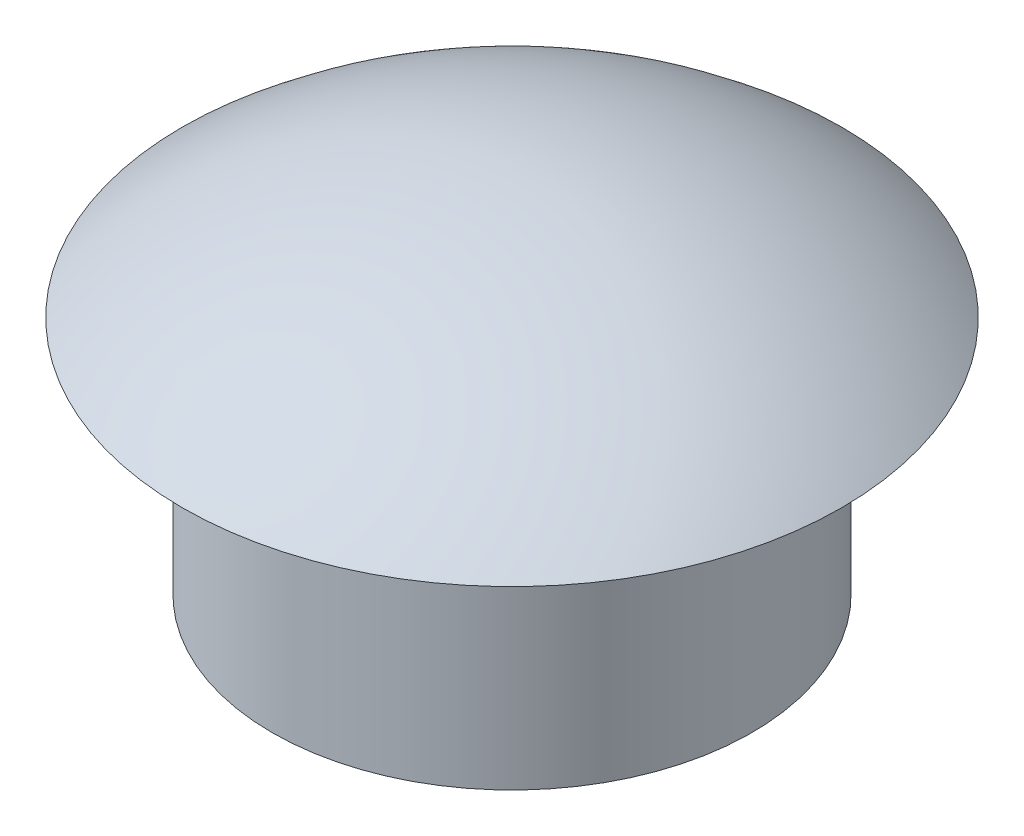
SolidWorks part; units mm, degrees
material "ABS PC"
ref_plane "Front Plane" through (0, 0, 0) normal (0, 0, 1) x (1, 0, 0)
ref_plane "Top Plane" through (0, 0, 0) normal (0, 1, 0) x (1, 0, 0)
ref_plane "Right Plane" through (0, 0, 0) normal (1, 0, 0) x (0, 0, -1)
sketch "Sketch1" plane through (0, 0, 0) normal (0, 1, 0) x (1, 0, 0)
  circle A0 centre (0, 0) radius 6.35
  circle A1 centre (0, 0) radius 4.7625
  dimension "D1" = 12.7
  dimension "D2" = 1.5875
extrude "Boss-Extrude1" add sketch "Sketch1" along normal blind 6.35
sketch "Sketch2" plane through (0, 0, 0) normal (0, 0, 1) x (1, 0, 0)
  line L0 (0, -55) -> (0, 55) construction
  line L1 (0, 9.525) -> (0, 6.35)
  line L2 (0, 6.35) -> (8.7312, 6.35)
  line L3 (6.35, 0) -> (6.35, 6.35) construction
  arc A0 (0, 9.525) -> (8.7312, 6.35) centre (0, -4.068) cw
  dimension "D1" = 3.175
  dimension "D2" = 2.3813
revolve "Revolve1" add sketch "Sketch2" angle 360 about L1
sketch "Sketch3" plane through (0, 0, 0) normal (0, 0, 1) x (1, 0, 0)
  line L0 (-6.35, 6.35) -> (6.35, 6.35) construction
  arc A0 (3.8623, 6.35) -> (-3.8623, 6.35) centre (0, 6.35) cw
  point P3 (0, 0)
  point P5 (0, 6.35)
  dimension "D1" = 3.8623
sketch "Sketch4" plane through (0, 6.35, 0) normal (0, -1, 0) x (1, 0, 0)
  circle A0 centre (3.8623, 0) radius 0.7937
  dimension "D1" = 1.5875
sweep "Sweep1" add profiles "Sketch4" path "Sketch3"
